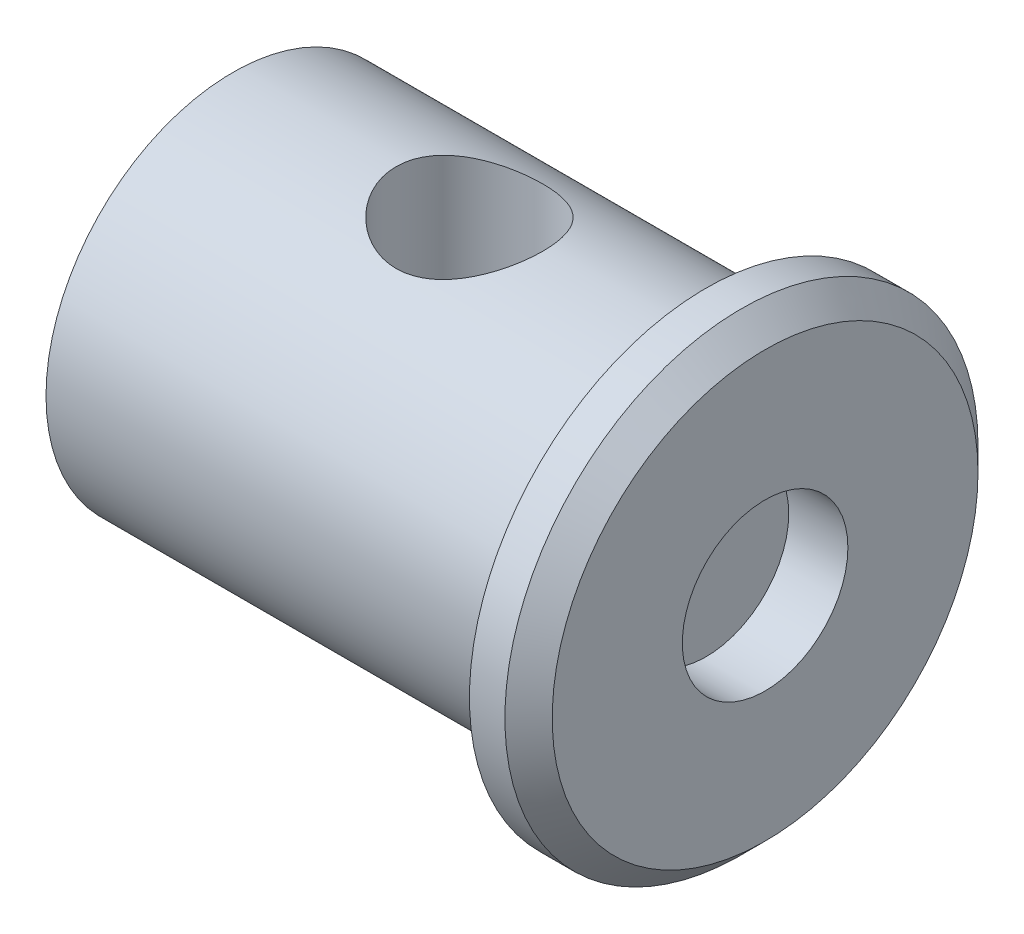
SolidWorks part; units mm, degrees
ref_plane "前视基准面" through (0, 0, 0) normal (0, 0, 1) x (1, 0, 0)
ref_plane "上视基准面" through (0, 0, 0) normal (0, 1, 0) x (1, 0, 0)
ref_plane "右视基准面" through (0, 0, 0) normal (1, 0, 0) x (0, 0, -1)
sketch "草图1" plane through (0, 0, 0) normal (1, 0, 0) x (0, 0, -1)
  circle A0 centre (0, 0) radius 7.9
extrude "凸台-拉伸1" add sketch "草图1" against normal blind 20
sketch "草图5" plane through (0, 0, 0) normal (0, 1, 0) x (1, 0, 0)
  line L0 (0, 0) -> (-10, 0) construction
  circle A0 centre (-10, 0) radius 3.1
extrude "切除-拉伸2" cut sketch "草图5" against normal mid plane 40 contours A0
sketch "草图6" plane through (0, 0, 0) normal (1, 0, 0) x (0, 0, -1)
  circle A0 centre (0, 0) radius 10
extrude "凸台-拉伸2" add sketch "草图6" along normal blind 2.5
sketch "草图7" plane through (2.5, 0, 0) normal (1, 0, 0) x (0, 0, -1)
  circle A0 centre (0, 0) radius 3.5
extrude "切除-拉伸3" cut sketch "草图7" against normal blind 2.5 contours A0
chamfer "倒角1" distance 1 angle 45 1 edges at (2.5, 0, -10)
